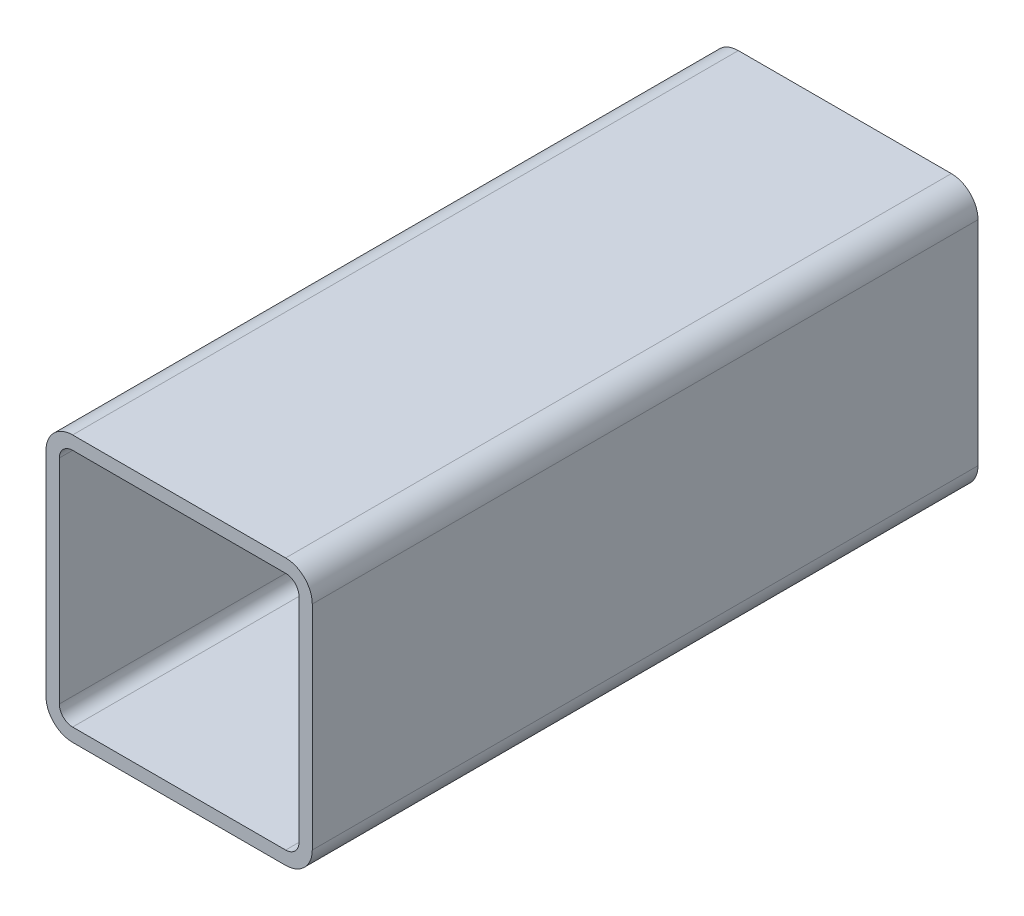
SolidWorks part; units mm, degrees
ref_plane "Front Plane" through (0, 0, 0) normal (0, 0, 1) x (1, 0, 0)
ref_plane "Top Plane" through (0, 0, 0) normal (0, 1, 0) x (1, 0, 0)
ref_plane "Right Plane" through (0, 0, 0) normal (1, 0, 0) x (0, 0, -1)
sketch "Sketch1" plane through (0, 0, 0) normal (0, 0, 1) x (1, 0, 0)
  line L0 (-18, 16) -> (-18, -16)
  line L1 (-16, 20) -> (16, 20)
  line L2 (-20, 16) -> (-20, -16)
  line L3 (-16, -20) -> (16, -20)
  line L4 (20, 16) -> (20, -16)
  line L5 (-20, 20) -> (20, -20) construction
  line L6 (-20, -20) -> (20, 20) construction
  line L7 (-16, -18) -> (16, -18)
  line L8 (18, 16) -> (18, -16)
  line L9 (-16, 18) -> (16, 18)
  arc A0 (-20, 16) -> (-16, 20) centre (-16, 16) cw
  arc A1 (-16, -20) -> (-20, -16) centre (-16, -16) cw
  arc A2 (20, -16) -> (16, -20) centre (16, -16) cw
  arc A3 (20, 16) -> (16, 20) centre (16, 16) ccw
  arc A4 (-16, -18) -> (-18, -16) centre (-16, -16) cw
  arc A5 (18, -16) -> (16, -18) centre (16, -16) cw
  arc A6 (18, 16) -> (16, 18) centre (16, 16) ccw
  arc A7 (-18, 16) -> (-16, 18) centre (-16, 16) cw
  point P0 (0, 0)
  dimension "D1" = 40
  dimension "D3" = 4
  dimension "D2" = 40
  dimension "D4" = 2
extrude "Boss-Extrude1" add sketch "Sketch1" along normal blind 100
sketch "Sketch2" plane through (0, 0, 0) normal (0, 1, 0) x (1, 0, 0)
  line L1 (0, -20) -> (0.1, -20)
  line L2 (0, -20) -> (0, -80)
  line L3 (0, -80) -> (0.1, -80)
  line L4 (0.1, -20) -> (0.1, -80)
  point P4 (0, 0)
  dimension "D1" = 0.1
  dimension "D2" = 20
extrude "Cut-Extrude1" cut sketch "Sketch2" along normal blind 0.5 from surface at -20 contours L2 L3 L4 L1 starting at face at (0, -20, 50)
sketch "Sketch3" plane through (0, 0, 0) normal (0, 1, 0) x (1, 0, 0)
  text T0 "Master 40x2 SHS" font "Century Gothic" height 3.5
extrude "Cut-Extrude2" cut sketch "Sketch3" along normal blind 0.5 from surface at -20 starting at face at (0, -20, 50)
